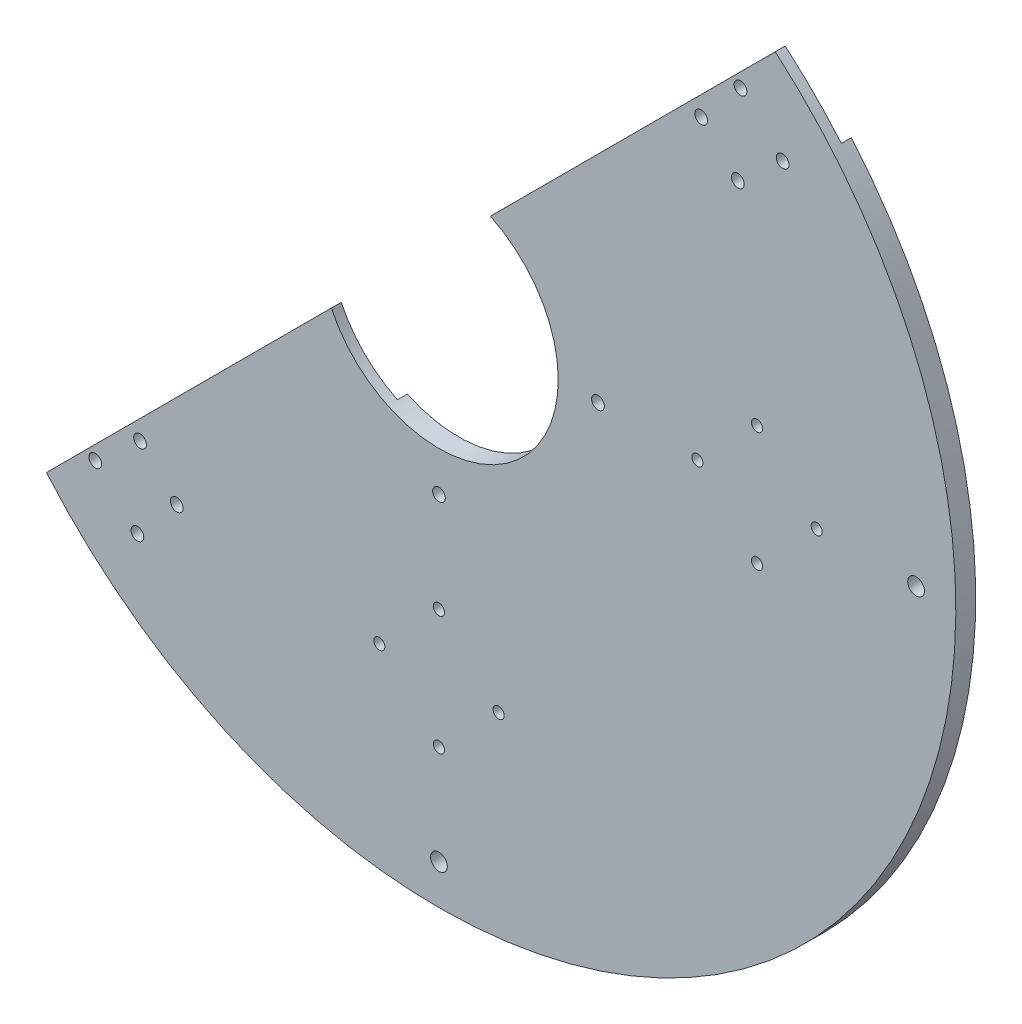
SolidWorks part; units mm, degrees
ref_plane "前视基准面" through (0, 0, 0) normal (0, 0, 1) x (1, 0, 0)
ref_plane "上视基准面" through (0, 0, 0) normal (0, 1, 0) x (1, 0, 0)
ref_plane "右视基准面" through (0, 0, 0) normal (1, 0, 0) x (0, 0, -1)
other "Configuration Table"
sketch "草图1" plane through (0, 0, 0) normal (0, 0, 1) x (1, 0, 0)
  circle A0 centre (0, 0) radius 120 construction
  circle A1 centre (0, 0) radius 40 construction
  circle A2 centre (0, 0) radius 30
  circle A3 centre (0, 0) radius 130
  circle A4 centre (0, 120) radius 2.1
  circle A5 centre (120, 0) radius 2.1
  circle A6 centre (0, -120) radius 2.1
  circle A7 centre (-120, 0) radius 2.1
  circle A8 centre (0, 40) radius 1.6
  circle A9 centre (40, 0) radius 1.6
  circle A10 centre (0, -40) radius 1.6
  circle A11 centre (-40, 0) radius 1.6
  point P17 (0, 0)
  point P26 (0, 0)
  dimension "D1" = 240
  dimension "D2" = 80
  dimension "D3" = 60
  dimension "D4" = 260
  dimension "D5" = 4.2
  dimension "D7" = 3.2
  dimension "D6" = 4
  dimension "D8" = 4
extrude "凸台-拉伸1" add sketch "草图1" along normal blind 5
sketch "草图2" plane through (0, 0, 5) normal (0, 0, 1) x (1, 0, 0)
  circle A0 centre (0, 80) radius 15 construction
  circle A1 centre (0, 95) radius 1.4
  circle A2 centre (15, 80) radius 1.4
  circle A3 centre (0, 80) radius 15 construction
  circle A4 centre (0, 65) radius 1.4
  circle A5 centre (0, 80) radius 15 construction
  circle A6 centre (-15, 80) radius 1.4
  circle A7 centre (0, 80) radius 15 construction
  circle A8 centre (95, 0) radius 1.4
  circle A9 centre (80, -15) radius 1.4
  circle A10 centre (65, 0) radius 1.4
  circle A11 centre (80, 15) radius 1.4
  circle A12 centre (80, 0) radius 15 construction
  circle A13 centre (80, 0) radius 15 construction
  circle A14 centre (80, 0) radius 15 construction
  circle A15 centre (80, 0) radius 15 construction
  circle A16 centre (0, -95) radius 1.4
  circle A17 centre (-15, -80) radius 1.4
  circle A18 centre (0, -65) radius 1.4
  circle A19 centre (15, -80) radius 1.4
  circle A20 centre (0, -80) radius 15 construction
  circle A21 centre (0, -80) radius 15 construction
  circle A22 centre (0, -80) radius 15 construction
  circle A23 centre (0, -80) radius 15 construction
  circle A24 centre (-95, 0) radius 1.4
  circle A25 centre (-80, 15) radius 1.4
  circle A26 centre (-65, 0) radius 1.4
  circle A27 centre (-80, -15) radius 1.4
  circle A28 centre (-80, 0) radius 15 construction
  circle A29 centre (-80, 0) radius 15 construction
  circle A30 centre (-80, 0) radius 15 construction
  circle A31 centre (-80, 0) radius 15 construction
  point P17 (0, 80)
  point P31 (80, 0)
  point P45 (0, -80)
  point P59 (-80, 0)
  point P60 (0, 0)
  dimension "D1" = 30
  dimension "D3" = 2.8
  dimension "D2" = 80
  dimension "D4" = 4
  dimension "D5" = 4
extrude "切除-拉伸1" cut sketch "草图2" against normal through all both and the other way through all
sketch "草图4" plane through (0, 0, 0) normal (0, 0, -1) x (-1, 0, 0)
  line L0 (0, 0) -> (-91.9239, 91.9239)
  line L1 (0, -1000) -> (0, 49000) construction
  circle A0 centre (0, 0) radius 130 construction
  dimension "D1" = 45
ref_plane "基准面1" through (91.9239, 91.9239, 0) normal (0.7071, 0.7071, 0) x (0, 0, -1)
sketch "草图5" plane through (91.9239, 91.9239, 0) normal (0.7071, 0.7071, 0) x (0, 0, -1)
  line L0 (-1000, 0) -> (49000, 0) construction
  line L1 (-2.5, -870) -> (-2.5, 49130) construction
  line L2 (0, 130) -> (-5, 130) construction
  line L3 (0, -10) -> (-2.5, -10)
  line L4 (0, -142128.463) -> (0, 176069.5885) construction
  line L5 (-2.5, -10) -> (-2.5, 10)
  line L6 (-2.5, 10) -> (-5, 10)
  line L7 (-5, 130) -> (-5, -130) construction
  line L8 (-5, 10) -> (-5, 130)
  line L9 (-5, 130) -> (0, 130)
  line L10 (0, 130) -> (0, -10)
  point P8 (-2.5, 130)
  dimension "D1" = 10
  dimension "D2" = 10
sketch "草图8" plane through (0, 0, 0) normal (0, 0, -1) x (-1, 0, 0)
  line L0 (-75.8409, 86.4475) -> (-86.4475, 75.8409) construction
  line L1 (0, 0) -> (-91.9239, 91.9239) construction
  line L2 (0, 0) -> (-35355.3391, 35355.3391) construction
  line L3 (-75.8409, 86.4475) -> (0, 0) construction
  line L4 (0, 0) -> (35355.3391, 35355.3391) construction
  line L5 (0, -201000) -> (0, 249000) construction
  line L6 (86.4475, -75.8409) -> (0, 0) construction
  line L7 (0, 0) -> (35355.3391, -35355.3391) construction
  line L8 (86.4475, -75.8409) -> (75.8409, -86.4475) construction
  circle A0 centre (-75.8409, 86.4475) radius 1.6
  arc A1 (-86.4475, 75.8409) -> (-81.3173, 81.3173) centre (0, 0) ccw construction
  circle A2 centre (-86.4475, 75.8409) radius 1.6
  circle A3 centre (0, 0) radius 100 construction
  circle A4 centre (-65.9486, 75.1717) radius 1.6
  circle A5 centre (-75.1717, 65.9486) radius 1.6
  arc A7 (75.8409, -86.4475) -> (81.3173, -81.3173) centre (0, 0) cw construction
  circle A8 centre (65.9486, -75.1717) radius 1.6
  circle A9 centre (75.1717, -65.9486) radius 1.6
  circle A10 centre (75.8409, -86.4475) radius 1.6
  circle A11 centre (86.4475, -75.8409) radius 1.6
  dimension "D2" = 3.2
  dimension "D3" = 230
  dimension "D4" = 3.2
  dimension "D5" = 200
  dimension "D6" = 3.2
  dimension "D1" = 15
  dimension "D7" = 45
extrude "切除-拉伸2" cut sketch "草图8" against normal up to next
extrude "切除-拉伸3" cut sketch "草图5" against normal through all
